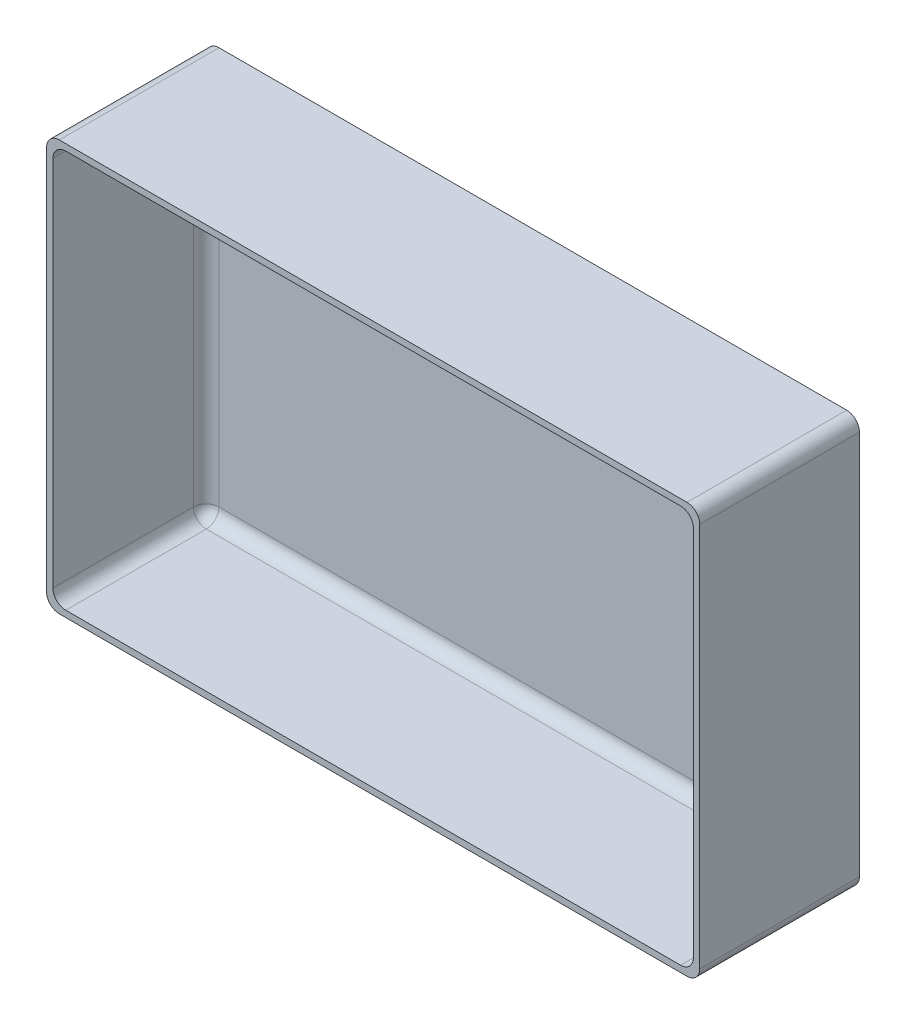
SolidWorks part; units mm, degrees
ref_plane "Plan de face" through (0, 0, 0) normal (0, 0, 1) x (1, 0, 0)
ref_plane "Plan de dessus" through (0, 0, 0) normal (0, 1, 0) x (1, 0, 0)
ref_plane "Plan de droite" through (0, 0, 0) normal (1, 0, 0) x (0, 0, -1)
sketch "Esquisse1" plane through (0, 0, 0) normal (0, 0, 1) x (1, 0, 0)
  line L1 (-40.9, 25.7) -> (40.9, 25.7)
  line L2 (-40.9, 25.7) -> (-40.9, -25.7)
  line L3 (-40.9, -25.7) -> (40.9, -25.7)
  line L4 (40.9, 25.7) -> (40.9, -25.7)
  line L5 (-40.9, 25.7) -> (40.9, -25.7) construction
  line L6 (-40.9, -25.7) -> (40.9, 25.7) construction
  point P0 (0, 0)
  dimension "D1" = 81.8
  dimension "D2" = 51.4
extrude "Boss.-Extru.1" add sketch "Esquisse1" along normal blind 20
shell "Coque1" thickness 0.8
fillet "Congé1" radius 1.6 12 edges at (40.1, 0, 0.8) (-40.1, 0, 0.8) (0, -24.9, 0.8) (40.1, -24.9, 10.4) (-40.1, -24.9, 10.4) (40.1, 24.9, 10.4) (0, 24.9, 0.8) (-40.1, 24.9, 10.4) (40.9, -25.7, 10) (-40.9, 25.7, 10) (40.9, 25.7, 10) (-40.9, -25.7, 10)
equation "\"longueur_ext\" = 80 + \"parois\" * 2 + 0.2"
equation "\"D1@Esquisse1\"=\"longueur_ext\""
equation "\"largeur_ext\"= 49.6 + \"parois\" * 2 + 0.2"
equation "\"D2@Esquisse1\"=\"largeur_ext\""
equation "\"profondeur_ext\"=20"
equation "\"D1@Boss.-Extru.1\"=\"profondeur_ext\""
equation "\"parois\"=0.8"
equation "\"D1@Coque1\"=\"parois\""
